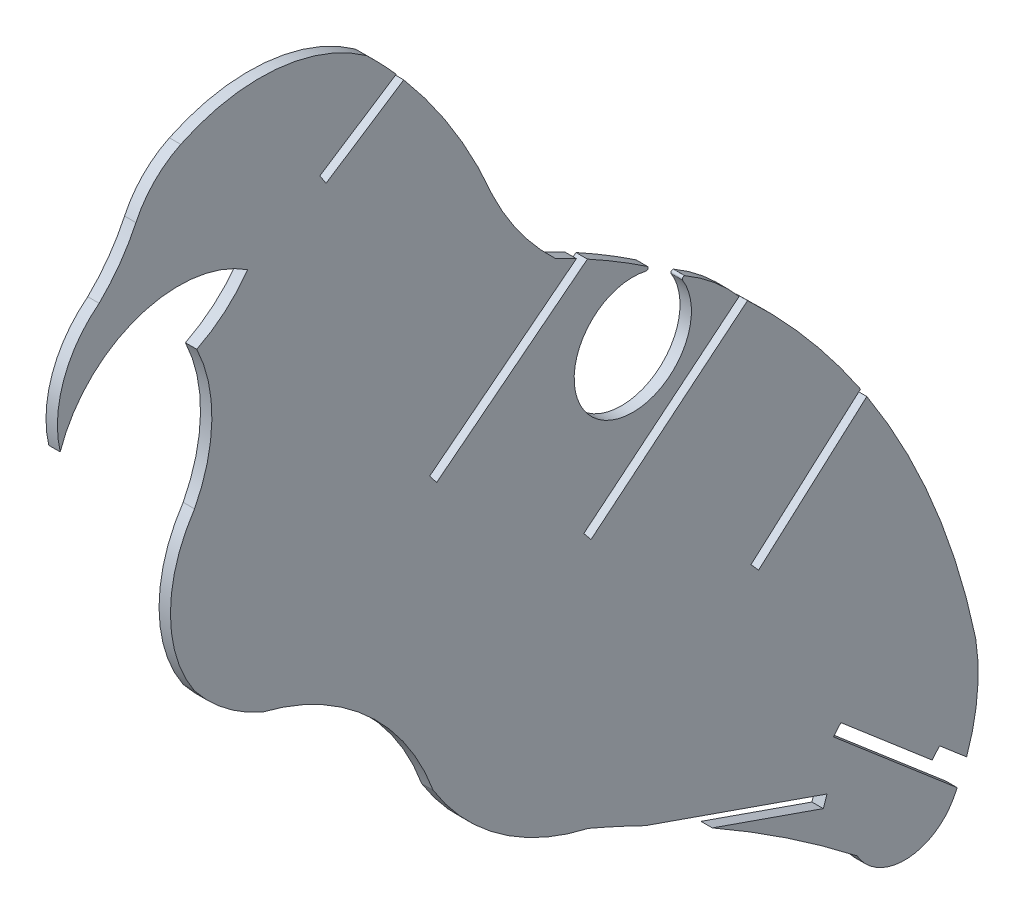
SolidWorks part; units mm, degrees
ref_plane "Front Plane" through (0, 0, 0) normal (0, 0, 1) x (1, 0, 0)
ref_plane "Top Plane" through (0, 0, 0) normal (0, 1, 0) x (1, 0, 0)
ref_plane "Right Plane" through (0, 0, 0) normal (1, 0, 0) x (0, 0, -1)
sketch "Sketch1" plane through (0, 0, 0) normal (1, 0, 0) x (0, 0, -1)
  line L0 (26.2948, -26.1121) -> (18.353, -32.3316) construction
  line L1 (13.4077, 17.1105) -> (3.1844, 10.4357)
  line L2 (42.3664, -85.975) -> (70.8387, -95.9128) construction
  line L3 (14.4156, 15.9485) -> (4.0176, 9.1596)
  line L4 (85.1662, -98.2973) -> (72.9422, -87.8436)
  line L5 (3.1844, 10.4357) -> (4.0176, 9.1596)
  line L6 (88.5272, -103.1769) -> (71.9517, -89.0018)
  line L7 (55.7328, -91.4474) -> (70.5876, -96.6322)
  line L8 (72.9422, -87.8436) -> (71.9517, -89.0018)
  line L10 (46.7571, -86.7005) -> (71.0898, -95.1933)
  line L11 (59.3227, -31.6144) -> (38.5213, -48.7044)
  line L12 (37.5363, -16.3404) -> (17.8832, -31.7317)
  line L13 (60.4511, -32.6597) -> (39.4887, -49.882)
  line L14 (39.005, -17.126) -> (18.8228, -32.9315)
  line L15 (77.391, -49.882) -> (61.4165, -64.0758) construction
  line L16 (17.8832, -31.7317) -> (18.8228, -32.9315)
  line L19 (38.5213, -48.7044) -> (39.4887, -49.882)
  line L22 (70.5876, -96.6322) -> (71.0898, -95.1933)
  line L23 (75.5707, -50.48) -> (60.9104, -63.5061)
  line L26 (76.4191, -51.7648) -> (61.9227, -64.6454)
  line L27 (89.7791, -100.2369) -> (86.1567, -97.1391)
  line L28 (60.9104, -63.5061) -> (61.9227, -64.6454)
  line L31 (85.1662, -98.2973) -> (86.1567, -97.1391)
  arc A0 (14.4156, 15.9485) -> (26.2948, -3.3559) centre (-42.4176, -32.3316) cw
  arc A1 (-21.4406, 17.3279) -> (-26.3696, 10.4357) centre (-42.4395, 27.1366) cw
  arc A2 (-15.4385, 23.3983) -> (-21.4406, 17.3279) centre (-9.934, 11.9532) ccw
  arc A3 (34.7231, -14.9186) -> (37.5363, -16.3404) centre (-10.7593, -108.4026) cw
  arc A4 (-13.596, -19.7882) -> (-13.596, -40.8997) centre (2.0459, -30.344) ccw
  arc A5 (-13.596, -40.8997) -> (-4.5225, -47.8952) centre (5.0384, -26.1121) ccw
  arc A6 (-4.5225, -47.8952) -> (18.353, -68.392) centre (-12.2977, -79.5863) cw
  arc A7 (18.353, -68.392) -> (39.1474, -83.2093) centre (46.367, -51.0775) ccw
  arc A8 (39.1474, -83.2093) -> (45.2574, -85.975) centre (-25.5765, -234.3296) cw
  arc A9 (90.9971, -87.1063) -> (89.7791, -100.2369) centre (64.6825, -91.2871) cw
  arc A10 (87.9409, -104.2865) -> (75.1047, -104.3688) centre (81.4995, -100.6863) cw
  arc A11 (88.5272, -103.1769) -> (87.9409, -104.2865) centre (64.6825, -91.2871) cw
  arc A12 (45.2574, -85.975) -> (46.7571, -86.7005) centre (-25.5765, -234.3296) cw
  arc A13 (52.1165, -25.6104) -> (59.3227, -31.6144) centre (37.865, -50.0421) cw
  arc A14 (39.005, -17.126) -> (47.0293, -21.9828) centre (-10.7593, -108.4026) cw
  arc A15 (60.4511, -32.6597) -> (70.0926, -43.0507) centre (-10.7593, -108.4026) cw
  arc A16 (55.7328, -91.4474) -> (75.1047, -104.3688) centre (-25.5765, -234.3296) cw
  arc A17 (76.4191, -51.7648) -> (90.9971, -87.1063) centre (-10.7593, -108.4026) cw
  arc A18 (46.8315, -22.4415) -> (51.7472, -25.9469) centre (45.082, -30.0942) ccw
  arc A19 (70.0926, -43.0507) -> (75.5707, -50.48) centre (-10.7593, -108.4026) cw
  arc A20 (51.7472, -25.9469) -> (52.1165, -25.6104) centre (51.9628, -25.8127) cw
  arc A21 (46.8315, -22.4415) -> (47.0293, -21.9828) centre (46.8881, -22.1939) ccw
  arc A58 (-15.4385, 23.3983) -> (9.4478, 21.2498) centre (-4.8104, 1.3) cw
  arc A64 (-26.3696, 10.4357) -> (-31.5819, -4.1915) centre (-17.6184, -0.9251) ccw
  arc A85 (9.4478, 21.2498) -> (13.4077, 17.1105) centre (-42.4176, -32.3316) cw
  arc A102 (-31.5819, -4.1915) -> (-6.4689, 4.378) centre (-15.7082, -9.6278) cw
  arc A103 (-6.4689, 4.378) -> (-13.2958, -1.4324) centre (-21.5911, 15.2297) cw
  arc A104 (-13.2958, -1.4324) -> (-13.596, -19.7882) centre (-31.7514, -10.311) cw
  arc A106 (26.2948, -3.3559) -> (34.7231, -14.9186) centre (61.4165, 13.3922) ccw
  point P31 (89.1913, -101.7396)
  point P39 (42.1153, -86.6945)
  point P56 (59.7894, -31.2309)
  point P58 (60.7569, -32.4084)
  point P63 (42.6175, -85.2556)
  point P69 (76.8848, -49.3123)
  point P71 (77.8971, -50.4516)
  point P75 (90.1818, -100.5814)
  point P76 (73.9327, -86.6853)
extrude "Boss-Extrude1" add sketch "Sketch1" along normal blind 1.524
